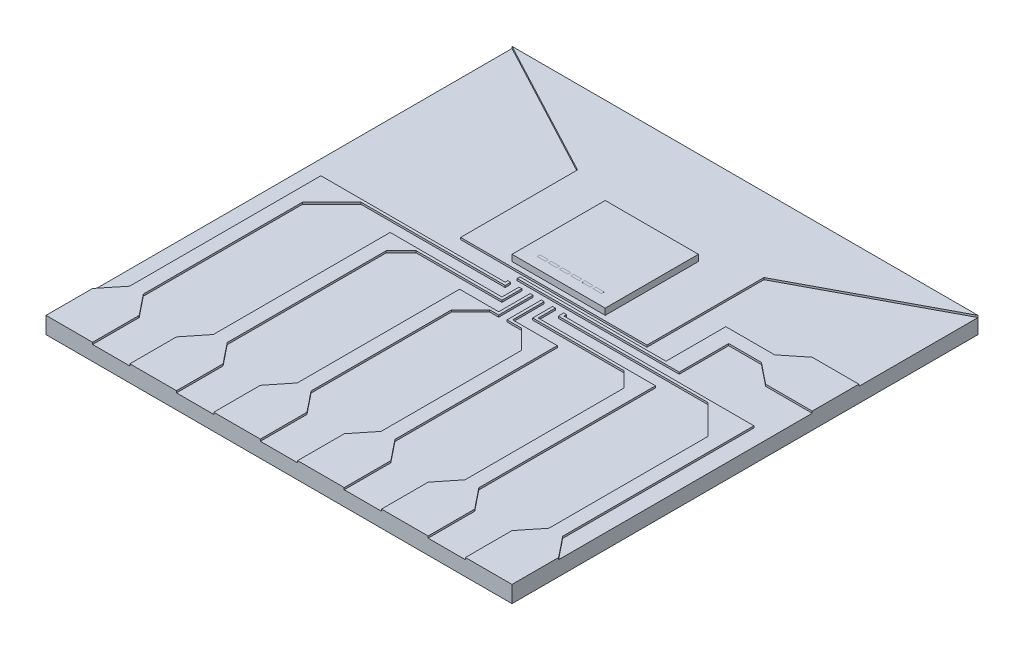
SolidWorks part; units mm, degrees
ref_plane "Front Plane" through (0, 0, 0) normal (0, 0, 1) x (1, 0, 0)
ref_plane "Top Plane" through (0, 0, 0) normal (0, 1, 0) x (1, 0, 0)
ref_plane "Right Plane" through (0, 0, 0) normal (1, 0, 0) x (0, 0, -1)
sketch "Sketch1" plane through (0, 0, 0) normal (0, 1, 0) x (1, 0, 0)
  line L0 (20.2388, 30.2687) -> (21.1388, 30.2687)
  line L5 (17.4888, 38.8187) -> (27.4888, 38.8187)
  line L6 (17.4888, 38.8187) -> (17.4888, 28.8187)
  line L7 (17.4888, 28.8187) -> (27.4888, 28.8187)
  line L8 (27.4888, 38.8187) -> (27.4888, 28.8187)
  line L9 (19.0388, 30.2687) -> (19.9388, 30.2687)
  line L10 (19.0388, 30.2687) -> (19.0388, 29.9687)
  line L11 (19.0388, 29.9687) -> (19.9388, 29.9687)
  line L12 (19.9388, 30.2687) -> (19.9388, 29.9687)
  line L13 (20.2388, 30.2687) -> (20.2388, 29.9687)
  line L14 (20.2388, 29.9687) -> (21.1388, 29.9687)
  line L15 (21.1388, 30.2687) -> (21.1388, 29.9687)
  line L16 (21.4388, 30.2687) -> (22.3388, 30.2687)
  line L17 (21.4388, 30.2687) -> (21.4388, 29.9687)
  line L18 (21.4388, 29.9687) -> (22.3388, 29.9687)
  line L19 (22.3388, 30.2687) -> (22.3388, 29.9687)
  line L20 (25.0388, 30.2687) -> (25.9388, 30.2687)
  line L21 (25.0388, 30.2687) -> (25.0388, 29.9687)
  line L22 (25.0388, 29.9687) -> (25.9388, 29.9687)
  line L23 (25.9388, 30.2687) -> (25.9388, 29.9687)
  line L24 (22.6388, 30.2687) -> (23.5388, 30.2687)
  line L25 (22.6388, 30.2687) -> (22.6388, 29.9687)
  line L26 (22.6388, 29.9687) -> (23.5388, 29.9687)
  line L27 (23.5388, 30.2687) -> (23.5388, 29.9687)
  line L28 (23.8388, 30.2687) -> (24.7388, 30.2687)
  line L29 (23.8388, 30.2687) -> (23.8388, 29.9687)
  line L30 (23.8388, 29.9687) -> (24.7388, 29.9687)
  line L31 (24.7388, 30.2687) -> (24.7388, 29.9687)
  line L32 (-2.5112, -1.1813) -> (47.4888, -1.1813)
  line L33 (-2.5112, 48.8187) -> (47.4888, 48.8187)
  line L34 (-2.5112, 48.8187) -> (-2.5112, -1.1813)
  line L36 (47.4888, 48.8187) -> (47.4888, -1.1813)
  line L41 (19.3388, 26.8187) -> (19.3388, 26.5368)
  line L42 (19.0388, 26.8187) -> (19.3388, 26.8187)
  line L43 (19.0388, 26.8187) -> (19.0388, 26.5368)
  line L58 (20.2388, 26.8187) -> (20.5388, 26.8187)
  line L59 (20.2388, 26.8187) -> (20.2388, 26.5368)
  line L62 (21.4388, 26.8187) -> (21.7388, 26.8187)
  line L63 (21.4388, 26.8187) -> (21.4388, 26.5368)
  line L66 (22.6388, 26.8187) -> (22.9388, 26.8187)
  line L67 (22.6388, 26.8187) -> (22.6388, 26.5368)
  line L70 (23.8388, 26.8187) -> (24.1388, 26.8187)
  line L71 (23.8388, 26.8187) -> (23.8388, 26.5368)
  line L74 (25.0388, 26.8187) -> (25.3388, 26.8187)
  line L75 (25.0388, 26.8187) -> (25.0388, 26.5368)
  line L78 (15.4888, 3.8187) -> (17.2483, 6.0171)
  line L79 (27.7293, 23.4368) -> (22.9388, 23.4368)
  line L80 (20.5388, 26.8187) -> (20.5388, 26.5368)
  line L81 (21.7388, 26.8187) -> (21.7388, 26.5368)
  line L82 (22.9388, 26.8187) -> (22.9388, 26.5368)
  line L83 (24.1388, 26.8187) -> (24.1388, 26.5368)
  line L84 (25.3388, 26.8187) -> (25.3388, 26.5368)
  line L86 (26.2483, 21.1022) -> (24.2136, 23.1368)
  line L87 (35.2483, 23.0817) -> (33.6431, 24.6868)
  line L89 (44.2483, 23.0817) -> (41.0931, 26.2368)
  line L92 (42.4888, 36.0333) -> (40.2439, 34.2392)
  line L97 (2.4888, -1.1813) -> (2.4888, 3.8187)
  line L99 (6.4888, -1.1813) -> (6.4888, 3.8187)
  line L101 (11.4888, -1.1813) -> (11.4888, 3.8187)
  line L103 (15.4888, -1.1813) -> (15.4888, 3.8187)
  line L105 (20.4888, -1.1813) -> (20.4888, 3.8187)
  line L109 (42.4888, -1.1813) -> (42.4888, 3.8187)
  line L111 (33.4888, 3.8187) -> (33.4888, -1.1813)
  line L113 (38.4888, 3.8187) -> (38.4888, -1.1813)
  line L115 (24.4888, -1.1813) -> (24.4888, 3.8187)
  line L117 (29.4888, -1.1813) -> (29.4888, 3.8187)
  line L130 (-2.5112, 3.8187) -> (-0.7359, 6.0171)
  line L131 (0.7293, 6.0171) -> (2.4888, 3.8187)
  line L132 (6.4888, 3.8187) -> (8.2455, 6.0171)
  line L133 (0.7293, 23.0817) -> (3.8844, 26.2368)
  line L135 (-0.7359, 6.0171) -> (-0.7359, 26.5368)
  line L136 (-0.7359, 26.5368) -> (0.7293, 26.5368)
  line L137 (0.7293, 6.0171) -> (0.7293, 23.0817)
  line L138 (0.7293, 26.5368) -> (19.0388, 26.5368)
  line L140 (3.8844, 26.2368) -> (19.3388, 26.2368)
  line L141 (19.3388, 26.5368) -> (19.3388, 26.2368)
  line L143 (9.7321, 6.0171) -> (11.4888, 3.8187)
  line L144 (18.7293, 6.0171) -> (20.4888, 3.8187)
  line L145 (9.7321, 23.0817) -> (11.3258, 24.6868)
  line L147 (20.2388, 26.5368) -> (20.2388, 24.9868)
  line L149 (20.5388, 26.5368) -> (20.5388, 24.9754)
  line L150 (20.2388, 24.9868) -> (8.2455, 24.9868)
  line L151 (20.5388, 24.9754) -> (20.5388, 24.6868)
  line L152 (20.5388, 24.6868) -> (11.3258, 24.6868)
  line L155 (8.2455, 6.0171) -> (8.2455, 24.9868)
  line L157 (9.7321, 6.0171) -> (9.7321, 23.0817)
  line L158 (24.4888, 3.8187) -> (26.2483, 6.0171)
  line L159 (27.7293, 6.0171) -> (29.4888, 3.8187)
  line L160 (33.4888, 3.8187) -> (35.2483, 6.0171)
  line L161 (36.7293, 6.0171) -> (38.4888, 3.8187)
  line L162 (42.4888, 3.8187) -> (44.2483, 6.0171)
  line L163 (45.7293, 6.0171) -> (47.4888, 3.8187)
  line L166 (21.4388, 26.5368) -> (21.4388, 23.4368)
  line L168 (21.7388, 26.5368) -> (21.7388, 23.4368)
  line L169 (21.4388, 23.4368) -> (17.2483, 23.4368)
  line L170 (21.7388, 23.4368) -> (21.7388, 23.1368)
  line L171 (21.7388, 23.1368) -> (20.766, 23.1368)
  line L175 (19.3388, 27.5187) -> (36.7293, 27.5187)
  line L176 (18.7313, 21.1022) -> (20.766, 23.1368)
  line L177 (18.7293, 6.0171) -> (18.7313, 6.0171)
  line L178 (17.2483, 6.0171) -> (17.2483, 23.4368)
  line L180 (18.7313, 6.0171) -> (18.7313, 21.1022)
  line L181 (22.6388, 26.5368) -> (22.6388, 23.1368)
  line L183 (22.9388, 26.5368) -> (22.9388, 23.4368)
  line L184 (22.6388, 23.1368) -> (24.2136, 23.1368)
  line L189 (26.2483, 6.0171) -> (26.2483, 21.1022)
  line L191 (27.7293, 6.0171) -> (27.7293, 23.4368)
  line L192 (23.8388, 26.5368) -> (23.8388, 24.6868)
  line L194 (24.1388, 26.5368) -> (24.1388, 24.9754)
  line L195 (23.8388, 24.6868) -> (33.6431, 24.6868)
  line L197 (24.1388, 24.9754) -> (35.0109, 24.9754)
  line L200 (35.2483, 6.0171) -> (35.2483, 23.0817)
  line L201 (35.2483, 24.9754) -> (36.7293, 24.9754)
  line L202 (36.7293, 6.0171) -> (36.7293, 24.9754)
  line L203 (35.0109, 24.9754) -> (35.2483, 24.9754)
  line L207 (25.0388, 26.5368) -> (25.0388, 26.2368)
  line L210 (25.0388, 26.2368) -> (41.0931, 26.2368)
  line L212 (25.3388, 26.5368) -> (45.7293, 26.5368)
  line L215 (44.2483, 6.0171) -> (44.2483, 23.0817)
  line L217 (45.7293, 6.0171) -> (45.7293, 26.5368)
  line L218 (19.3388, 27.5187) -> (19.3388, 27.8187)
  line L219 (19.3388, 27.8187) -> (35.0109, 27.8187)
  line L221 (47.4888, 36.0333) -> (42.4888, 36.0333)
  line L223 (47.4888, 31.0333) -> (42.4888, 31.0333)
  line L225 (40.2439, 32.8275) -> (42.4888, 31.0333)
  line L226 (-2.5112, 48.8187) -> (12.4888, 40.8516)
  line L228 (40.2439, 34.2392) -> (35.0109, 34.2392)
  line L230 (40.2439, 32.8275) -> (36.7293, 32.8275)
  line L233 (35.0109, 34.2392) -> (35.0109, 27.8187)
  line L235 (36.7293, 32.8275) -> (36.7293, 27.5187)
  line L236 (12.4888, 40.8516) -> (12.4888, 28.3022)
  line L237 (12.4888, 28.3022) -> (32.4888, 28.3022)
  line L238 (32.4888, 40.8516) -> (32.4888, 28.3022)
  line L239 (47.4888, 48.8187) -> (32.4888, 40.8516)
  point P85 (21.7388, 26.6777)
  dimension "D1" = 20
  dimension "D2" = 20
  dimension "D3" = 10
  dimension "D4" = 50
  dimension "D5" = 2
  dimension "D6" = 0.3
  dimension "D7" = 0.3
  dimension "D8" = 0.3
  dimension "D9" = 0.3
  dimension "D10" = 0.3
  dimension "D11" = 0.3
  dimension "D12" = 5
  dimension "D13" = 5
  dimension "D14" = 4
  dimension "D15" = 5
  dimension "D16" = 5
  dimension "D17" = 4
  dimension "D18" = 5
  dimension "D19" = 5
  dimension "D20" = 5
  dimension "D21" = 4
  dimension "D22" = 5
  dimension "D23" = 5
  dimension "D24" = 5
  dimension "D25" = 4
  dimension "D26" = 0.3
  dimension "D27" = 0.3
  dimension "D28" = 0.9
  dimension "D29" = 0.9
  dimension "D30" = 0.9
  dimension "D31" = 0.9
  dimension "D32" = 0.9
  dimension "D33" = 22.15
  dimension "D34" = 1.25
  dimension "D35" = 5
  dimension "D36" = 1.25
  dimension "D37" = 1
  dimension "D38" = 5
  dimension "D39" = 5
  dimension "D40" = 5
sketch "Sketch2" plane through (0, 0, 0) normal (0, 1, 0) x (1, 0, 0)
  line L0 (-2.5112, 3.8187) -> (-0.7359, 6.0171)
  line L1 (-2.5112, 48.8187) -> (47.4888, 48.8187)
  line L2 (-2.5112, 48.8187) -> (-2.5112, -1.1813)
  line L3 (-2.5112, -1.1813) -> (47.4888, -1.1813)
  line L4 (47.4888, 48.8187) -> (47.4888, -1.1813)
  line L5 (-0.7359, 6.0171) -> (-0.7359, 26.5368)
  line L6 (-0.7359, 26.5368) -> (19.0388, 26.5368)
  line L7 (19.0388, 26.5368) -> (19.0388, 26.8187)
  line L8 (19.0388, 26.8187) -> (19.3388, 26.8187)
  line L9 (19.3388, 26.8187) -> (19.3388, 26.2368)
  line L10 (19.3388, 26.2368) -> (3.8844, 26.2368)
  line L11 (3.8844, 26.2368) -> (0.7293, 23.0817)
  line L12 (0.7293, 23.0817) -> (0.7293, 6.0171)
  line L13 (0.7293, 6.0171) -> (2.4888, 3.8187)
  line L14 (2.4888, 3.8187) -> (2.4888, -1.1813)
  line L15 (2.4888, -1.1813) -> (-2.5112, -1.1813)
  line L16 (11.4888, -1.1813) -> (6.4888, -1.1813)
  line L17 (6.4888, -1.1813) -> (6.4888, 3.8187)
  line L18 (6.4888, 3.8187) -> (8.2455, 6.0171)
  line L19 (8.2455, 6.0171) -> (8.2455, 24.9868)
  line L20 (8.2455, 24.9868) -> (20.2388, 24.9868)
  line L21 (20.2388, 24.9868) -> (20.2388, 26.8187)
  line L22 (20.2388, 26.8187) -> (20.5388, 26.8187)
  line L23 (20.5388, 26.8187) -> (20.5388, 24.6868)
  line L24 (20.5388, 24.6868) -> (11.3258, 24.6868)
  line L25 (11.3258, 24.6868) -> (9.7321, 23.0817)
  line L26 (9.7321, 23.0817) -> (9.7321, 6.0171)
  line L27 (9.7321, 6.0171) -> (11.4888, 3.8187)
  line L28 (11.4888, 3.8187) -> (11.4888, -1.1813)
  line L29 (20.4888, -1.1813) -> (15.4888, -1.1813)
  line L30 (15.4888, -1.1813) -> (15.4888, 3.8187)
  line L31 (15.4888, 3.8187) -> (17.2483, 6.0171)
  line L32 (17.2483, 6.0171) -> (17.2483, 23.4368)
  line L33 (17.2483, 23.4368) -> (21.4388, 23.4368)
  line L34 (21.4388, 23.4368) -> (21.4388, 26.8187)
  line L35 (21.4388, 26.8187) -> (21.7388, 26.8187)
  line L36 (21.7388, 26.8187) -> (21.7388, 23.1368)
  line L37 (21.7388, 23.1368) -> (20.766, 23.1368)
  line L38 (20.766, 23.1368) -> (18.7313, 21.1022)
  line L39 (18.7313, 21.1022) -> (18.7293, 6.0171)
  line L40 (18.7293, 6.0171) -> (20.4888, 3.8187)
  line L41 (20.4888, 3.8187) -> (20.4888, -1.1813)
  line L42 (29.4888, -1.1813) -> (24.4888, -1.1813)
  line L43 (24.4888, -1.1813) -> (24.4888, 3.8187)
  line L44 (24.4888, 3.8187) -> (26.2483, 6.0171)
  line L45 (26.2483, 6.0171) -> (26.2483, 21.1022)
  line L46 (26.2483, 21.1022) -> (24.2136, 23.1368)
  line L47 (24.2136, 23.1368) -> (22.6388, 23.1368)
  line L48 (22.6388, 23.1368) -> (22.6388, 26.8187)
  line L49 (22.6388, 26.8187) -> (22.9388, 26.8187)
  line L50 (22.9388, 26.8187) -> (22.9388, 23.4368)
  line L51 (22.9388, 23.4368) -> (27.7293, 23.4368)
  line L52 (27.7293, 23.4368) -> (27.7293, 6.0171)
  line L53 (27.7293, 6.0171) -> (29.4888, 3.8187)
  line L54 (29.4888, 3.8187) -> (29.4888, -1.1813)
  line L55 (38.4888, -1.1813) -> (33.4888, -1.1813)
  line L56 (33.4888, -1.1813) -> (33.4888, 3.8187)
  line L57 (33.4888, 3.8187) -> (35.2483, 6.0171)
  line L58 (35.2483, 6.0171) -> (35.2483, 23.0817)
  line L59 (35.2483, 23.0817) -> (33.6431, 24.6868)
  line L60 (33.6431, 24.6868) -> (23.8388, 24.6868)
  line L61 (23.8388, 24.6868) -> (23.8388, 26.8187)
  line L62 (23.8388, 26.8187) -> (24.1388, 26.8187)
  line L63 (24.1388, 26.8187) -> (24.1388, 24.9754)
  line L64 (24.1388, 24.9754) -> (36.7293, 24.9754)
  line L65 (36.7293, 24.9754) -> (36.7293, 6.0171)
  line L66 (36.7293, 6.0171) -> (38.4888, 3.8187)
  line L67 (38.4888, 3.8187) -> (38.4888, -1.1813)
  line L68 (42.4888, -1.1813) -> (42.4888, 3.8187)
  line L69 (42.4888, 3.8187) -> (44.2483, 6.0171)
  line L70 (44.2483, 6.0171) -> (44.2483, 23.0817)
  line L71 (44.2483, 23.0817) -> (41.0931, 26.2368)
  line L72 (41.0931, 26.2368) -> (25.0388, 26.2368)
  line L73 (25.0388, 26.2368) -> (25.0388, 26.8187)
  line L74 (25.0388, 26.8187) -> (25.3388, 26.8187)
  line L75 (25.3388, 26.8187) -> (25.3388, 26.5368)
  line L76 (25.3388, 26.5368) -> (45.7293, 26.5368)
  line L77 (45.7293, 26.5368) -> (45.7293, 6.0171)
  line L78 (45.7293, 6.0171) -> (47.4888, 3.8187)
  line L79 (47.4888, 3.8187) -> (47.4888, -1.1813)
  line L80 (42.4888, -1.1813) -> (42.4888, 3.8187)
  line L81 (36.7293, 27.5187) -> (19.3388, 27.5187)
  line L82 (19.3388, 27.5187) -> (19.3388, 27.8187)
  line L83 (19.3388, 27.8187) -> (35.0109, 27.8187)
  line L84 (35.0109, 27.8187) -> (35.0109, 34.2392)
  line L85 (35.0109, 34.2392) -> (40.2439, 34.2392)
  line L86 (40.2439, 34.2392) -> (42.4888, 36.0333)
  line L87 (42.4888, 36.0333) -> (47.4888, 36.0333)
  line L88 (47.4888, 36.0333) -> (47.4888, 31.0333)
  line L89 (47.4888, 31.0333) -> (42.4888, 31.0333)
  line L90 (42.4888, 31.0333) -> (40.2439, 32.8275)
  line L91 (40.2439, 32.8275) -> (36.7293, 32.8275)
  line L92 (36.7293, 32.8275) -> (36.7293, 27.5187)
  line L93 (-2.5112, 48.8187) -> (12.4888, 40.8516)
  line L94 (12.4888, 40.8516) -> (12.4888, 28.3022)
  line L95 (12.4888, 28.3022) -> (32.4888, 28.3022)
  line L96 (32.4888, 28.3022) -> (32.4888, 40.8516)
  line L97 (32.4888, 40.8516) -> (47.4888, 48.8187)
  line L98 (47.4888, 48.8187) -> (-2.5112, 48.8187)
sketch "Sketch3" plane through (0, 0, 0) normal (0, 1, 0) x (1, 0, 0)
  line L1 (-2.5112, 48.8187) -> (47.4888, 48.8187)
  line L2 (-2.5112, 48.8187) -> (-2.5112, -1.1813)
  line L3 (-2.5112, -1.1813) -> (47.4888, -1.1813)
  line L4 (47.4888, 48.8187) -> (47.4888, -1.1813)
extrude "Boss-Extrude1" add sketch "Sketch3" against normal blind 1.5875
extrude "Boss-Extrude2" add sketch "Sketch2" along normal blind 0.2043 contours L96 L97 L1 L93 L94 L95 | L92 L91 L90 L89 L4 L87 L86 L85 L84 L83 L82 L81 | L78 L77 L76 L75 L74 L73 L72 L71 L70 L69 L68 L3 L4 | L67 L66 L65 L64 L63 L62 L61 L60 L59 L58 L57 L56 L3 | L54 L53 L52 L51 L50 L49 L48 L47 L46 L45 L44 L43 L3 | L41 L40 L39 L38 L37 L36 L35 L34 L33 L32 L31 L30 L3 | L28 L27 L26 L25 L24 L23 L22 L21 L20 L19 L18 L17 L3 | L14 L13 L12 L11 L10 L9 L8 L7 L6 L5 L0 L2 L3
sketch "Sketch4" plane through (0, 0.2043, 0) normal (0, 1, 0) x (1, 0, 0)
  line L1 (17.4888, 38.8187) -> (27.4888, 38.8187)
  line L2 (17.4888, 38.8187) -> (17.4888, 28.8187)
  line L3 (17.4888, 28.8187) -> (27.4888, 28.8187)
  line L4 (27.4888, 38.8187) -> (27.4888, 28.8187)
extrude "Boss-Extrude3" add sketch "Sketch4" along normal blind 0.675
sketch "Sketch5" plane through (0, 0.8793, 0) normal (0, 1, 0) x (1, 0, 0)
  line L1 (19.0388, 30.2687) -> (19.9388, 30.2687)
  line L2 (19.0388, 30.2687) -> (19.0388, 29.9687)
  line L3 (19.0388, 29.9687) -> (19.9388, 29.9687)
  line L4 (19.9388, 30.2687) -> (19.9388, 29.9687)
  line L5 (20.2388, 30.2687) -> (21.1388, 30.2687)
  line L6 (20.2388, 30.2687) -> (20.2388, 29.9687)
  line L7 (20.2388, 29.9687) -> (21.1388, 29.9687)
  line L8 (21.1388, 30.2687) -> (21.1388, 29.9687)
  line L9 (21.4388, 30.2687) -> (22.3388, 30.2687)
  line L10 (21.4388, 30.2687) -> (21.4388, 29.9687)
  line L11 (21.4388, 29.9687) -> (22.3388, 29.9687)
  line L12 (22.3388, 30.2687) -> (22.3388, 29.9687)
  line L13 (22.6388, 30.2687) -> (23.5388, 30.2687)
  line L14 (22.6388, 30.2687) -> (22.6388, 29.9687)
  line L15 (22.6388, 29.9687) -> (23.5388, 29.9687)
  line L16 (23.5388, 30.2687) -> (23.5388, 29.9687)
  line L17 (23.8388, 30.2687) -> (24.7388, 30.2687)
  line L18 (23.8388, 30.2687) -> (23.8388, 29.9687)
  line L19 (23.8388, 29.9687) -> (24.7388, 29.9687)
  line L20 (24.7388, 30.2687) -> (24.7388, 29.9687)
  line L21 (25.0388, 30.2687) -> (25.9388, 30.2687)
  line L22 (25.0388, 30.2687) -> (25.0388, 29.9687)
  line L23 (25.0388, 29.9687) -> (25.9388, 29.9687)
  line L24 (25.9388, 30.2687) -> (25.9388, 29.9687)
extrude "Boss-Extrude4" add sketch "Sketch5" along normal blind 0.001
